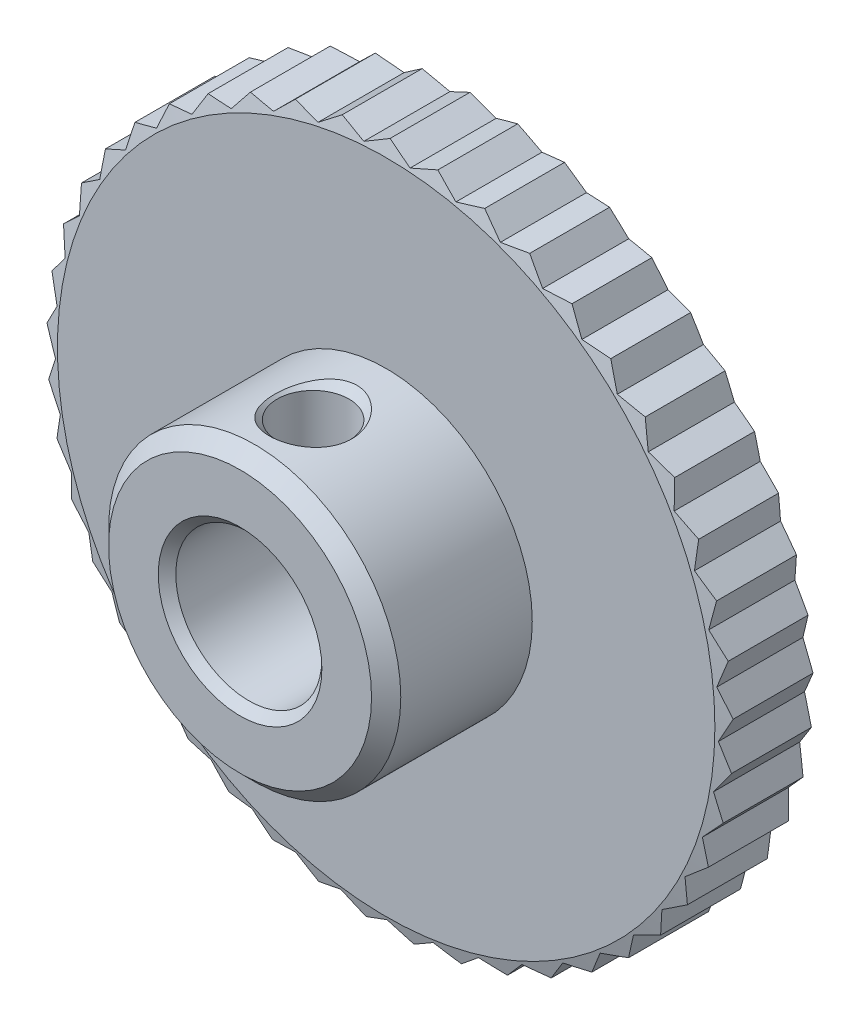
SolidWorks part; units mm, degrees
material "Delrin 2700 NC010, Low Viscosity Acetal Copolymer (SS)"
ref_plane "Front Plane" through (0, 0, 0) normal (0, 0, 1) x (1, 0, 0)
ref_plane "Top Plane" through (0, 0, 0) normal (0, 1, 0) x (1, 0, 0)
ref_plane "Right Plane" through (0, 0, 0) normal (1, 0, 0) x (0, 0, -1)
ref_plane "Plane1" through (0, 0, 0) normal (1, 0, 0) x (0, 0, -1)
sketch "Sketch1" plane through (0, 0, 0) normal (1, 0, 0) x (0, 0, -1)
  line L0 (-8, 2.8) -> (-7.7, 2.5)
  line L1 (-7.7, 2.5) -> (-0.3, 2.5)
  line L2 (-0.3, 2.5) -> (0, 2.8)
  line L3 (0, 2.8) -> (0, 11.25)
  line L4 (0, 11.25) -> (-0.4019, 12.75)
  line L5 (-0.4019, 12.75) -> (-2.5981, 12.75)
  line L6 (-2.5981, 12.75) -> (-3, 11.25)
  line L7 (-3, 11.25) -> (-3, 5)
  line L8 (-3, 5) -> (-7.5, 5)
  line L9 (-7.5, 5) -> (-8, 4.5)
  line L10 (-8, 4.5) -> (-8, 2.8)
  line L11 (0, 0) -> (-8, 0) construction
revolve "Revolve1" add sketch "Sketch1" angle 360 about L11
ref_plane "Plane2" through (0, 0, 0) normal (0, 0, 1) x (1, 0, 0)
sketch "Sketch2" plane through (0, 0, 0) normal (0, 0, 1) x (1, 0, 0)
  line L0 (-11.7428, 0.4101) -> (-11.3431, -0.3961)
  line L1 (-11.3431, -0.3961) -> (-11.6856, -1.2282)
  line L2 (-11.6856, -1.2282) -> (-11.1776, -1.9709)
  line L3 (-11.1776, -1.9709) -> (-11.401, -2.8426)
  line L4 (-11.401, -2.8426) -> (-10.7945, -3.5073)
  line L5 (-10.7945, -3.5073) -> (-10.8944, -4.4016)
  line L6 (-10.8944, -4.4016) -> (-10.2013, -4.9755)
  line L7 (-10.2013, -4.9755) -> (-10.1758, -5.875)
  line L8 (-10.1758, -5.875) -> (-9.4096, -6.3468)
  line L9 (-9.4096, -6.3468) -> (-9.2591, -7.234)
  line L10 (-9.2591, -7.234) -> (-8.4347, -7.5946)
  line L11 (-8.4347, -7.5946) -> (-8.1622, -8.4522)
  line L12 (-8.1622, -8.4522) -> (-7.2956, -8.6946)
  line L13 (-7.2956, -8.6946) -> (-6.9065, -9.5059)
  line L14 (-6.9065, -9.5059) -> (-6.0146, -9.6253)
  line L15 (-6.0146, -9.6253) -> (-5.5163, -10.3746)
  line L16 (-5.5163, -10.3746) -> (-4.6165, -10.3687)
  line L17 (-4.6165, -10.3687) -> (-4.0187, -11.0414)
  line L18 (-4.0187, -11.0414) -> (-3.1285, -10.9103)
  line L19 (-3.1285, -10.9103) -> (-2.443, -11.4932)
  line L20 (-2.443, -11.4932) -> (-1.5796, -11.2395)
  line L21 (-1.5796, -11.2395) -> (-0.8196, -11.7214)
  line L22 (-0.8196, -11.7214) -> (0, -11.35)
  line L23 (0, -11.35) -> (0.8196, -11.7214)
  line L24 (0.8196, -11.7214) -> (1.5796, -11.2395)
  line L25 (1.5796, -11.2395) -> (2.443, -11.4932)
  line L26 (2.443, -11.4932) -> (3.1285, -10.9103)
  line L27 (3.1285, -10.9103) -> (4.0187, -11.0414)
  line L28 (4.0187, -11.0414) -> (4.6165, -10.3687)
  line L29 (4.6165, -10.3687) -> (5.5163, -10.3746)
  line L30 (5.5163, -10.3746) -> (6.0146, -9.6253)
  line L31 (6.0146, -9.6253) -> (6.9065, -9.5059)
  line L32 (6.9065, -9.5059) -> (7.2956, -8.6946)
  line L33 (7.2956, -8.6946) -> (8.1622, -8.4522)
  line L34 (8.1622, -8.4522) -> (8.4347, -7.5946)
  line L35 (8.4347, -7.5946) -> (9.2591, -7.234)
  line L36 (9.2591, -7.234) -> (9.4096, -6.3468)
  line L37 (9.4096, -6.3468) -> (10.1758, -5.875)
  line L38 (10.1758, -5.875) -> (10.2013, -4.9755)
  line L39 (10.2013, -4.9755) -> (10.8944, -4.4016)
  line L40 (10.8944, -4.4016) -> (10.7945, -3.5073)
  line L41 (10.7945, -3.5073) -> (11.401, -2.8426)
  line L42 (11.401, -2.8426) -> (11.1776, -1.9709)
  line L43 (11.1776, -1.9709) -> (11.6856, -1.2282)
  line L44 (11.6856, -1.2282) -> (11.3431, -0.3961)
  line L45 (11.3431, -0.3961) -> (11.7428, 0.4101)
  line L46 (11.7428, 0.4101) -> (11.2878, 1.1864)
  line L47 (11.2878, 1.1864) -> (11.5715, 2.0404)
  line L48 (11.5715, 2.0404) -> (11.0129, 2.7458)
  line L49 (11.0129, 2.7458) -> (11.1749, 3.6309)
  line L50 (11.1749, 3.6309) -> (10.5235, 4.2518)
  line L51 (10.5235, 4.2518) -> (10.5608, 5.1509)
  line L52 (10.5608, 5.1509) -> (9.8294, 5.675)
  line L53 (9.8294, 5.675) -> (9.7412, 6.5705)
  line L54 (9.7412, 6.5705) -> (8.9439, 6.9878)
  line L55 (8.9439, 6.9878) -> (8.732, 7.8623)
  line L56 (8.732, 7.8623) -> (7.8844, 8.1645)
  line L57 (7.8844, 8.1645) -> (7.5528, 9.001)
  line L58 (7.5528, 9.001) -> (6.6714, 9.1823)
  line L59 (6.6714, 9.1823) -> (6.2266, 9.9646)
  line L60 (6.2266, 9.9646) -> (5.3285, 10.0215)
  line L61 (5.3285, 10.0215) -> (4.7792, 10.7342)
  line L62 (4.7792, 10.7342) -> (3.8819, 10.6655)
  line L63 (3.8819, 10.6655) -> (3.2387, 11.2948)
  line L64 (3.2387, 11.2948) -> (2.3598, 11.102)
  line L65 (2.3598, 11.102) -> (1.6353, 11.6356)
  line L66 (1.6353, 11.6356) -> (0.7917, 11.3224)
  line L67 (0.7917, 11.3224) -> (0, 11.75)
  line L68 (0, 11.75) -> (-0.7917, 11.3224)
  line L69 (-0.7917, 11.3224) -> (-1.6353, 11.6356)
  line L70 (-1.6353, 11.6356) -> (-2.3598, 11.102)
  line L71 (-2.3598, 11.102) -> (-3.2387, 11.2948)
  line L72 (-3.2387, 11.2948) -> (-3.8819, 10.6655)
  line L73 (-3.8819, 10.6655) -> (-4.7792, 10.7342)
  line L74 (-4.7792, 10.7342) -> (-5.3285, 10.0215)
  line L75 (-5.3285, 10.0215) -> (-6.2266, 9.9646)
  line L76 (-6.2266, 9.9646) -> (-6.6714, 9.1823)
  line L77 (-6.6714, 9.1823) -> (-7.5528, 9.001)
  line L78 (-7.5528, 9.001) -> (-7.8844, 8.1645)
  line L79 (-7.8844, 8.1645) -> (-8.732, 7.8623)
  line L80 (-8.732, 7.8623) -> (-8.9439, 6.9878)
  line L81 (-8.9439, 6.9878) -> (-9.7412, 6.5705)
  line L82 (-9.7412, 6.5705) -> (-9.8294, 5.675)
  line L83 (-9.8294, 5.675) -> (-10.5608, 5.1509)
  line L84 (-10.5608, 5.1509) -> (-10.5235, 4.2518)
  line L85 (-10.5235, 4.2518) -> (-11.1749, 3.6309)
  line L86 (-11.1749, 3.6309) -> (-11.0129, 2.7458)
  line L87 (-11.0129, 2.7458) -> (-11.5715, 2.0404)
  line L88 (-11.5715, 2.0404) -> (-11.2878, 1.1864)
  line L89 (-11.2878, 1.1864) -> (-11.7428, 0.4101)
  circle A0 centre (0, 0) radius 23.5
extrude "Cut-Extrude1" cut sketch "Sketch2" along normal blind 3
ref_plane "Plane3" through (0, 0, 5.5) normal (0, 0, 1) x (1, 0, 0)
sketch "Sketch3" plane through (0, 0, 5.5) normal (0, 0, 1) x (1, 0, 0)
  line L0 (0, 0) -> (-1.5, 0)
  line L1 (-1.5, 0) -> (-1.5, 2.5)
  line L2 (-1.5, 2.5) -> (-1.2295, 2.7705)
  line L3 (-1.2295, 2.7705) -> (-1.2295, 4.7295)
  line L4 (-1.2295, 4.7295) -> (-1.5, 5)
  line L5 (-1.5, 5) -> (-1.5, 10)
  line L6 (-1.5, 10) -> (0, 10)
  line L7 (0, 10) -> (0, 0)
  line L8 (0, 10) -> (0, 0) construction
revolve "Cut-Revolve1" cut sketch "Sketch3" angle 360 about L8
